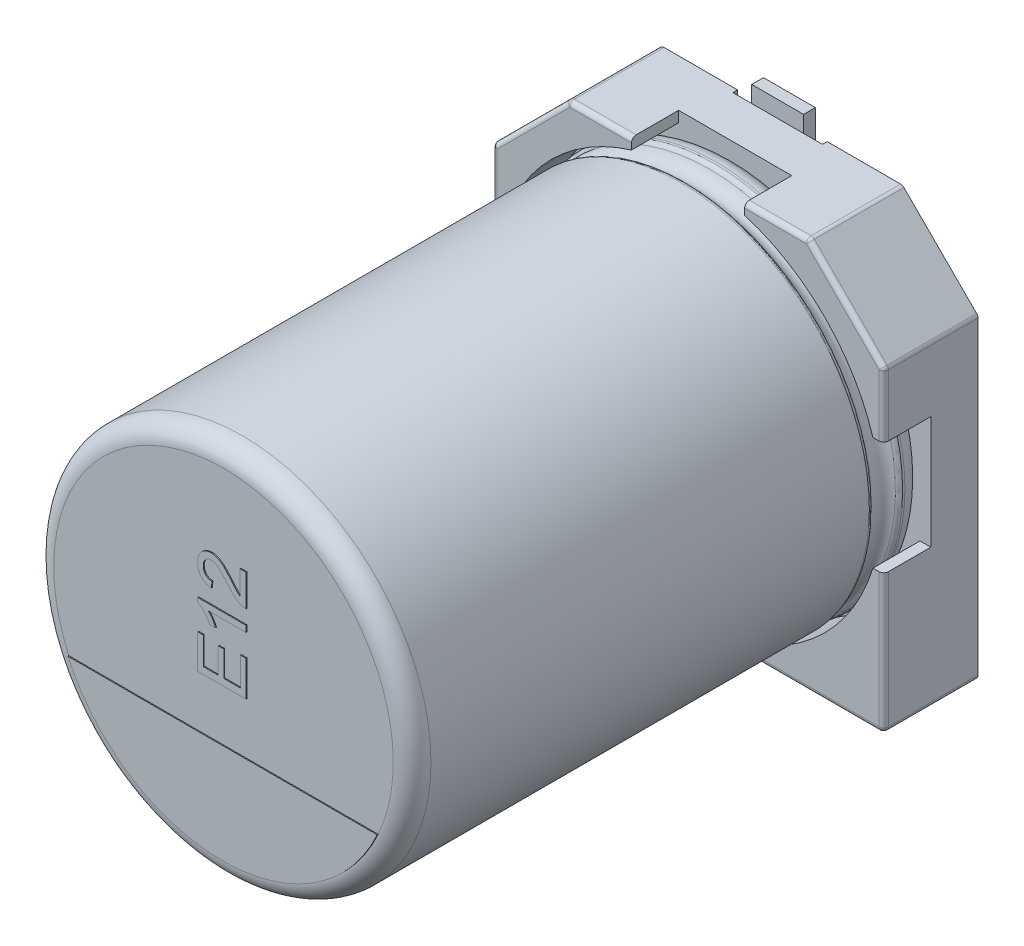
SolidWorks part; units mm, degrees
ref_plane "Plan de face" through (0, 0, 0) normal (0, 0, 1) x (1, 0, 0)
ref_plane "Plan de dessus" through (0, 0, 0) normal (0, 1, 0) x (1, 0, 0)
ref_plane "Plan de droite" through (0, 0, 0) normal (1, 0, 0) x (0, 0, -1)
sketch "Sketch2" plane through (0, 0, 0) normal (0, 0, 1) x (1, 0, 0)
  line L0 (-4.15, 2.55) -> (-2.55, 4.15)
  line L1 (-2.55, 4.15) -> (2.55, 4.15)
  line L2 (-4.15, 2.55) -> (-4.15, -4.15)
  line L3 (-4.15, -4.15) -> (4.15, -4.15)
  line L4 (4.15, 2.55) -> (4.15, -4.15)
  line L5 (-4.15, 4.15) -> (4.15, -4.15) construction
  line L6 (-4.15, -4.15) -> (4.15, 4.15) construction
  line L7 (2.55, 4.15) -> (4.15, 2.55)
  point P0 (0, 0)
  dimension "D1" = 8.3
  dimension "D2" = 8.3
extrude "Boss-Extrude1" add sketch "Sketch2" along normal blind 1
sketch "Sketch4" plane through (0, 0, 1) normal (0, 0, 1) x (1, 0, 0)
  line L0 (-4.15, 2.55) -> (-2.55, 4.15)
  line L1 (-2.55, 4.15) -> (-1.2, 4.15)
  line L3 (-4.15, 1.2) -> (-4.15, 2.55)
  line L4 (2.55, 4.15) -> (4.15, 2.55)
  line L5 (4.15, 2.55) -> (4.15, 1.2)
  line L6 (4.15, -4.15) -> (4.15, 2.55) construction
  line L7 (2.55, 4.15) -> (-2.55, 4.15) construction
  line L8 (1.2, 4.15) -> (2.55, 4.15)
  line L9 (-4.15, -4.15) -> (4.15, -4.15) construction
  line L10 (4.15, -1.2) -> (4.15, -4.15)
  line L11 (4.15, -4.15) -> (1.2, -4.15)
  line L12 (-4.15, -1.2) -> (-4.15, -4.15)
  line L13 (-4.15, -4.15) -> (-1.2, -4.15)
  line L14 (-4.946, -1.2) -> (4.946, -1.2) construction
  line L15 (-4.8253, 1.2) -> (5.0249, 1.2) construction
  line L16 (3.9205, 1.2) -> (4.15, 1.2)
  line L17 (3.9205, -1.2) -> (4.15, -1.2)
  line L18 (-3.9205, -1.2) -> (-4.15, -1.2)
  line L19 (-3.9205, 1.2) -> (-4.15, 1.2)
  line L20 (-1.2, 5.0139) -> (-1.2, -5.2906) construction
  line L21 (1.2, 5.0139) -> (1.2, -5.4) construction
  line L22 (-1.2, 4.15) -> (-1.2, 3.9205)
  line L23 (1.2, 4.15) -> (1.2, 3.9205)
  line L24 (-1.2, -3.9205) -> (-1.2, -4.15)
  line L25 (1.2, -3.9205) -> (1.2, -4.15)
  arc A0 (-1.2, 3.9205) -> (-3.9205, 1.2) centre (0, 0) ccw construction
  arc A1 (-3.9205, 1.2) -> (-1.2, 3.9205) centre (0, 0) cw
  arc A2 (1.2, 3.9205) -> (3.9205, 1.2) centre (0, 0) cw
  arc A3 (1.2, -3.9205) -> (3.9205, -1.2) centre (0, 0) ccw
  arc A4 (-1.2, -3.9205) -> (-3.9205, -1.2) centre (0, 0) cw
  arc A5 (3.9205, 1.2) -> (1.2, 3.9205) centre (0, 0) ccw construction
  arc A6 (1.2, -3.9205) -> (3.9205, -1.2) centre (0, 0) ccw construction
  arc A7 (-3.9205, -1.2) -> (-1.2, -3.9205) centre (0, 0) ccw construction
  point P33 (0, -1.2)
  dimension "D1" = 8.2
  dimension "D2" = 1.2
  dimension "D3" = 1.2
  dimension "D4" = 1.2
  dimension "D5" = 1.2
sketch "Sketch5" plane through (0, 0, 0) normal (0, 0, 1) x (1, 0, 0)
extrude "Boss-Extrude2" add sketch "Sketch4" along normal blind 1
sketch "Sketch7" plane through (0, 0, 0) normal (0, 0, -1) x (1, 0, 0)
  line L1 (-2.9065, 2.8449) -> (2.9065, 2.8449) construction
  line L2 (-2.9065, 2.8449) -> (-2.9065, -2.8449) construction
  line L3 (-2.9065, -2.8449) -> (2.9065, -2.8449) construction
  line L4 (2.9065, 2.8449) -> (2.9065, -2.8449) construction
  line L5 (-2.9065, 2.8449) -> (2.9065, -2.8449) construction
  line L6 (-2.9065, -2.8449) -> (2.9065, 2.8449) construction
  circle A0 centre (-2.9065, 2.8449) radius 0.35
  circle A1 centre (2.9065, 2.8449) radius 0.35
  circle A2 centre (-2.9065, -2.8449) radius 0.35
  circle A3 centre (2.9065, -2.8449) radius 0.35
  point P0 (0, 0)
  point P10 (2.9065, 2.8449)
  dimension "D1" = 0.7
  dimension "D2" = 0.7
  dimension "D3" = 0.7
  dimension "D4" = 0.7
extrude "Spacer Pad" add sketch "Sketch7" along normal blind 0.15
sketch "Sketch8" plane through (0, 0, 0) normal (0, 0, -1) x (1, 0, 0)
  line L0 (-0.95, 4.3618) -> (-0.95, -4.4479) construction
  line L1 (0.95, 4.3618) -> (0.95, -4.4479) construction
  dimension "D1" = 0.95
  dimension "D2" = 1.9
sketch "Sketch9" plane through (0, 0, 0) normal (0, 0, -1) x (1, 0, 0)
  line L0 (-4.6239, -1.5) -> (5.0007, -1.5) construction
  line L1 (-4.6239, 1.5) -> (5.2975, 1.5) construction
  line L2 (-0.95, 4.3618) -> (-0.95, -4.4479) construction
  line L3 (-0.95, 1.5) -> (0.95, 1.5)
  line L4 (-0.95, 1.5) -> (-0.95, 4.15)
  line L5 (-0.95, 4.15) -> (0.95, 4.15)
  line L6 (0.95, 1.5) -> (0.95, 4.15)
  line L7 (0.95, 4.3618) -> (0.95, -4.4479) construction
  line L8 (-4.15, 4.15) -> (4.15, 4.15) construction
  line L9 (2.55, -4.15) -> (-2.55, -4.15) construction
  line L10 (-0.95, -1.5) -> (0.95, -1.5)
  line L11 (-0.95, -1.5) -> (-0.95, -4.15)
  line L12 (-0.95, -4.15) -> (0.95, -4.15)
  line L13 (0.95, -1.5) -> (0.95, -4.15)
  dimension "D1" = 1.5
  dimension "D2" = 1.5
extrude "Cut-Extrude1" cut sketch "Sketch9" against normal blind 0.1
fillet "Fillet1" radius 0.1 6 edges at (-4.15, 2.55, 1) (-2.55, 4.15, 1) (2.55, 4.15, 1) (4.15, 2.55, 1) (4.15, -4.15, 1) (-4.15, -4.15, 1)
sketch "Sketch10" plane through (0, 0, 0) normal (1, 0, 0) x (0, 0, -1)
  line L0 (18.9631, 0) -> (-18.9631, 0) construction
  line L2 (-11.8536, 0) -> (-11.8536, 3.6)
  line L3 (-11.4536, 4) -> (-2.1546, 4)
  line L4 (-1, 3.6) -> (-1, 0)
  line L7 (-1.4494, 4) -> (-1.4, 4)
  arc A0 (-11.8536, 3.6) -> (-11.4536, 4) centre (-11.4536, 3.6) cw
  arc A1 (-1.4, 4) -> (-1, 3.6) centre (-1.4, 3.6) cw
  arc A2 (-1.5413, 3.9394) -> (-2.0626, 3.9394) centre (-1.802, 4.051) cw
  arc A3 (-2.0626, 3.9394) -> (-2.1546, 4) centre (-2.1546, 3.9) ccw
  arc A4 (-1.5413, 3.9394) -> (-1.4494, 4) centre (-1.4494, 3.9) cw
  point P4 (0, 0)
  point P9 (0, 0)
  point P12 (-9.3847, 4)
  point P13 (-11.8536, 4)
  point P22 (-11.418, 4)
  dimension "D2" = 0.4
  dimension "D3" = 0.4
  dimension "D4" = 0.1
  dimension "D5" = 0.1
  dimension "D1" = 4
revolve "Revolve1" add sketch "Sketch10" angle 360 about L0
fillet "Fillet2" radius 0.1 16 edges at (2.625, -4.15, 2) (4.1207, -4.1207, 2) (4.15, 1.8543, 2) (4.1424, 2.5468, 2) (1.8543, 4.15, 2) (2.5468, 4.1424, 2) (-1.8543, 4.15, 2) (-2.5468, 4.1424, 2) (-3.35, 3.35, 2) (-4.1424, 2.5468, 2) (-4.15, -2.625, 2) (-4.1207, -4.1207, 2) (4.15, -2.625, 2) (3.35, 3.35, 2) (-4.15, 1.8543, 2) (-2.625, -4.15, 2)
sketch "Sketch13" plane through (0, 0, 11.8536) normal (0, 0, 1) x (1, 0, 0)
  line L0 (-5.2631, -1.4818) -> (3.7173, -1.4818) construction
  line L1 (-3.2809, -1.4818) -> (3.2809, -1.4818)
  arc A0 (3.2809, -1.4818) -> (-3.2809, -1.4818) centre (0, 0) cw
  point P3 (-0.7729, -1.4818)
extrude "Cathode marker" add sketch "Sketch13" along normal blind 0.02
sketch "Sketch15" plane through (0, 0, 11.8536) normal (0, 0, 1) x (1, 0, 0)
  line L1 (0.5, 2.1812) -> (0.5, -0.5) construction
  text T1 "E12" font "Arial" height in points 4
extrude "Text" add sketch "Sketch15" along normal blind 0.02
sketch "Sketch18" plane through (0, 0, 0.1) normal (0, 0, -1) x (1, 0, 0)
  line L0 (0, 5.1012) -> (0, -5.1012) construction
  point P4 (0, 0)
sketch "Sketch19" plane through (0, 0, 0.1) normal (0, 0, -1) x (1, 0, 0)
  line L0 (-1.0534, -4.5) -> (1.0534, -4.5) construction
  line L2 (-0.95, -4.15) -> (0.95, -4.15) construction
  line L3 (-1.9391, 4.5) -> (1.9391, 4.5) construction
  line L5 (0.95, 4.15) -> (-0.95, 4.15) construction
  line L6 (0, 5.1012) -> (0, -5.1012) construction
  line L7 (-0.55, 1.6) -> (0.55, 1.6)
  line L8 (-0.55, 1.6) -> (-0.55, 4.5)
  line L9 (-0.55, 4.5) -> (0.55, 4.5)
  line L10 (0.55, 1.6) -> (0.55, 4.5)
  line L11 (-0.55, 1.6) -> (0.55, 4.5) construction
  line L12 (-0.55, 4.5) -> (0.55, 1.6) construction
  line L14 (-0.55, -1.6) -> (0.55, -1.6)
  line L15 (-0.55, -1.6) -> (-0.55, -4.5)
  line L16 (-0.55, -4.5) -> (0.55, -4.5)
  line L17 (0.55, -1.6) -> (0.55, -4.5)
  line L18 (-0.55, -1.6) -> (0.55, -4.5) construction
  line L19 (-0.55, -4.5) -> (0.55, -1.6) construction
  point P3 (0, -4.5)
  point P8 (0, 4.5)
  point P10 (0, 3.05)
  point P17 (0, -3.05)
  dimension "D1" = 0.35
  dimension "D2" = 0.35
  dimension "D3" = 1.1
  dimension "D4" = 2.9
  dimension "D5" = 1.1
  dimension "D6" = 2.9
extrude "Boss-Extrude6" add sketch "Sketch19" along normal blind 0.25
